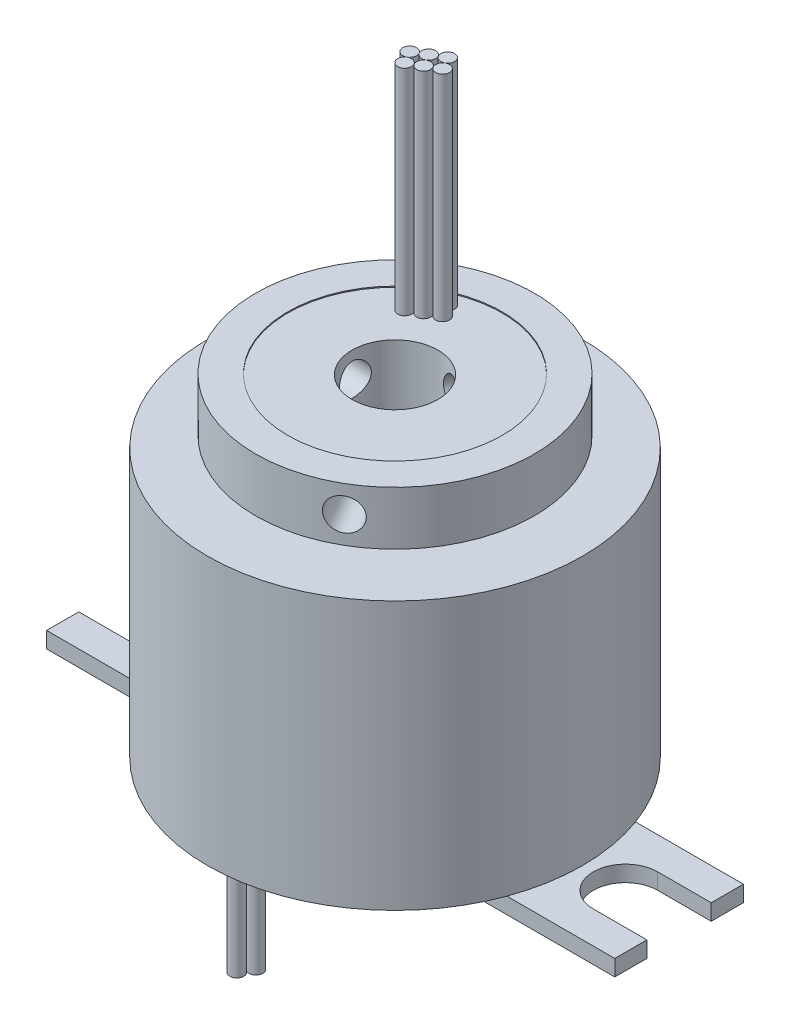
SolidWorks part; units mm, degrees
ref_plane "Front" through (0, 0, 0) normal (0, 0, 1) x (1, 0, 0)
ref_plane "Top" through (0, 0, 0) normal (0, 1, 0) x (1, 0, 0)
ref_plane "Right" through (0, 0, 0) normal (1, 0, 0) x (0, 0, -1)
sketch "草图1" plane through (0, 0, 0) normal (0, 1, 0) x (1, 0, 0)
  circle A0 centre (0, 0) radius 17.5
  dimension "D1" = 35
extrude "凸台-拉伸1" add sketch "草图1" along normal blind 25
sketch "草图2" plane through (0, 25, 0) normal (0, 1, 0) x (1, 0, 0)
  circle A0 centre (0, 0) radius 10
  dimension "D1" = 20
extrude "凸台-拉伸2" add sketch "草图2" along normal blind 1
sketch "草图3" plane through (0, 26, 0) normal (0, 1, 0) x (1, 0, 0)
  circle A0 centre (0, 0) radius 13
  dimension "D1" = 26
extrude "凸台-拉伸3" add sketch "草图3" along normal blind 5
sketch "草图4" plane through (0, 31, 0) normal (0, 1, 0) x (1, 0, 0)
  circle A0 centre (0, 0) radius 4
  dimension "D1" = 8
extrude "切除-拉伸1" cut sketch "草图4" against normal blind 47
sketch "草图5" plane through (0, 0, 0) normal (1, 0, 0) x (0, 0, -1)
  circle A0 centre (0, 28.5) radius 1.5
  dimension "D1" = 3
extrude "切除-拉伸2" cut sketch "草图5" against normal blind 47
sketch "草图6" plane through (0, 0, 0) normal (1, 0, 0) x (0, 0, -1)
  line L0 (0, 39.0808) -> (0, -7.08) construction
pattern_circular "阵列(圆周)1" count 3 every 120 about axis through (0, 39.0808, 0) along (0, -1, 0) of "切除-拉伸2"
sketch "草图8" plane through (0, 31, 0) normal (0, 1, 0) x (1, 0, 0)
  circle A2 centre (0, 0) radius 10
  circle A3 centre (0, 0) radius 13 construction
  dimension "D1" = 3
extrude "切除-拉伸3" cut sketch "草图8" against normal blind 0.1
sketch "草图9" plane through (0, 30.9, 0) normal (0, 1, 0) x (1, 0, 0)
  circle A6 centre (-5.4236, 6.7939) radius 0.645
  circle A7 centre (-4.2977, 7.4439) radius 0.645
  circle A8 centre (-3.1719, 8.0939) radius 0.645
  circle A9 centre (-4.7736, 5.668) radius 0.645
  circle A10 centre (-3.6477, 6.318) radius 0.645
  circle A11 centre (-2.5219, 6.968) radius 0.645
  dimension "D1" = 1.29
  dimension "D2" = 1.29
  dimension "D3" = 1.29
  dimension "D4" = 1.29
  dimension "D5" = 1.29
  dimension "D6" = 1.29
extrude "凸台-拉伸4" add sketch "草图9" along normal blind 20
sketch "草图10" plane through (0, 0, 0) normal (0, -1, 0) x (1, 0, 0)
  line L0 (0, -14) -> (0, 14) construction
  circle A0 centre (0, 0) radius 14 construction
  circle A1 centre (0.65, 13.6247) radius 0.645
  circle A2 centre (-0.65, 13.6247) radius 0.645
  circle A3 centre (0, 14.7506) radius 0.645
  circle A4 centre (0.65, -14.3753) radius 0.645
  circle A5 centre (-0.65, -14.3753) radius 0.645
  circle A6 centre (0, -13.2494) radius 0.645
  point P17 (0, 14)
  point P30 (0, -14)
  dimension "D1" = 1.29
  dimension "D2" = 1.29
  dimension "D3" = 1.29
  dimension "D4" = 1.29
  dimension "D5" = 1.29
  dimension "D6" = 1.29
extrude "凸台-拉伸5" add sketch "草图10" along normal blind 10
sketch "草图11" plane through (0, 0, 0) normal (0, -1, 0) x (1, 0, 0)
  line L0 (-20.2353, 0) -> (19.9684, 0) construction
  line L1 (-26.5, 3) -> (-21.5, 3)
  line L2 (-26.5, -6) -> (-11.5, -6)
  line L3 (-26.5, -6) -> (-26.5, -3)
  line L4 (-26.5, 6) -> (-11.5, 6)
  line L5 (-11.5, -6) -> (-11.5, 6)
  line L6 (-26.5, -6) -> (-11.5, 6) construction
  line L7 (-26.5, 6) -> (-11.5, -6) construction
  line L8 (0, -10.2057) -> (0, 10.8355) construction
  line L9 (-21.5, -3) -> (-26.5, -3)
  line L10 (-26.5, 3) -> (-26.5, 6)
  line L11 (11.5, -6) -> (11.5, 6)
  line L12 (26.5, -6) -> (11.5, -6)
  line L13 (26.5, -6) -> (26.5, -3)
  line L14 (21.5, -3) -> (26.5, -3)
  line L15 (26.5, 3) -> (21.5, 3)
  line L16 (26.5, 3) -> (26.5, 6)
  line L17 (26.5, 6) -> (11.5, 6)
  arc A0 (-21.5, -3) -> (-21.5, 3) centre (-21.5, 0) ccw
  arc A1 (21.5, -3) -> (21.5, 3) centre (21.5, 0) cw
  point P2 (-19, 0)
  dimension "D7" = 6
  dimension "D1" = 26.5
  dimension "D2" = 15
  dimension "D3" = 12
  dimension "D4" = 3
  dimension "D5" = 3
extrude "凸台-拉伸6" add sketch "草图11" along normal blind 1.5
